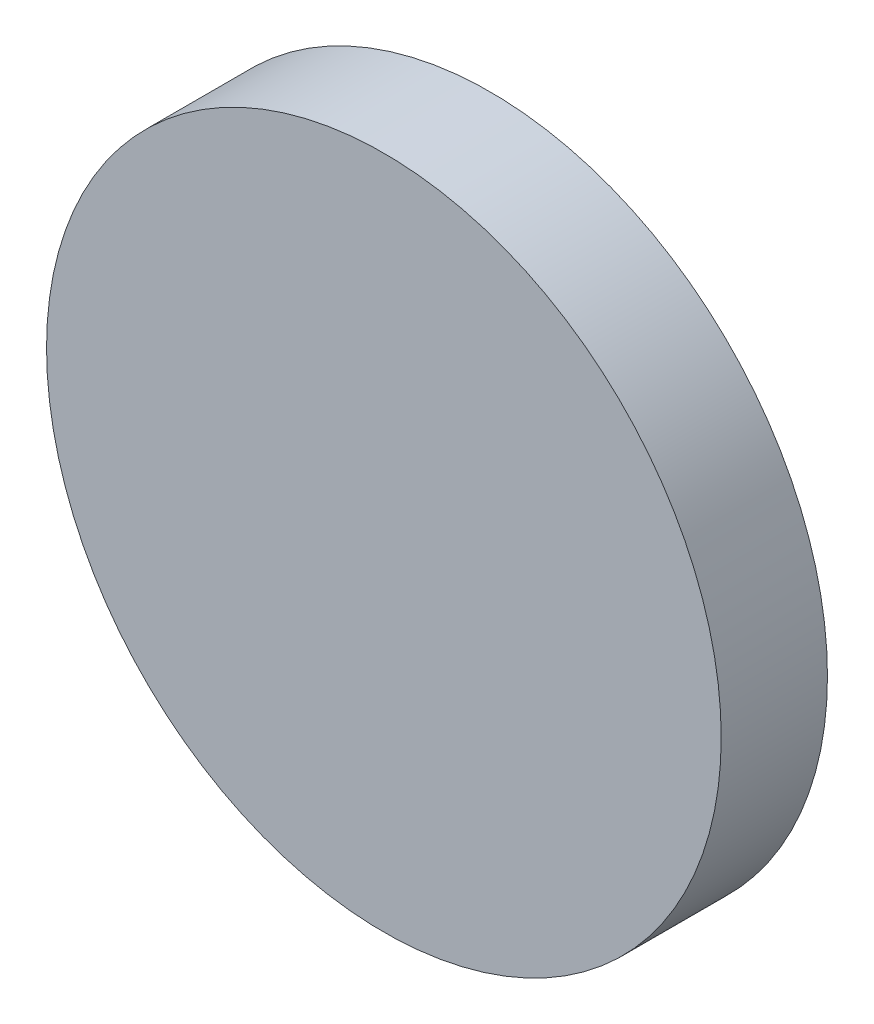
SolidWorks part; units mm, degrees
ref_plane "前视基准面" through (0, 0, 0) normal (0, 0, 1) x (1, 0, 0)
ref_plane "上视基准面" through (0, 0, 0) normal (0, 1, 0) x (1, 0, 0)
ref_plane "右视基准面" through (0, 0, 0) normal (1, 0, 0) x (0, 0, -1)
sketch "草图1" plane through (0, 0, 0) normal (0, 0, 1) x (1, 0, 0)
  circle A0 centre (0, 0) radius 6.35
  dimension "D1" = 12.7
extrude "凸台-拉伸1" add sketch "草图1" along normal blind 2 contours A0
